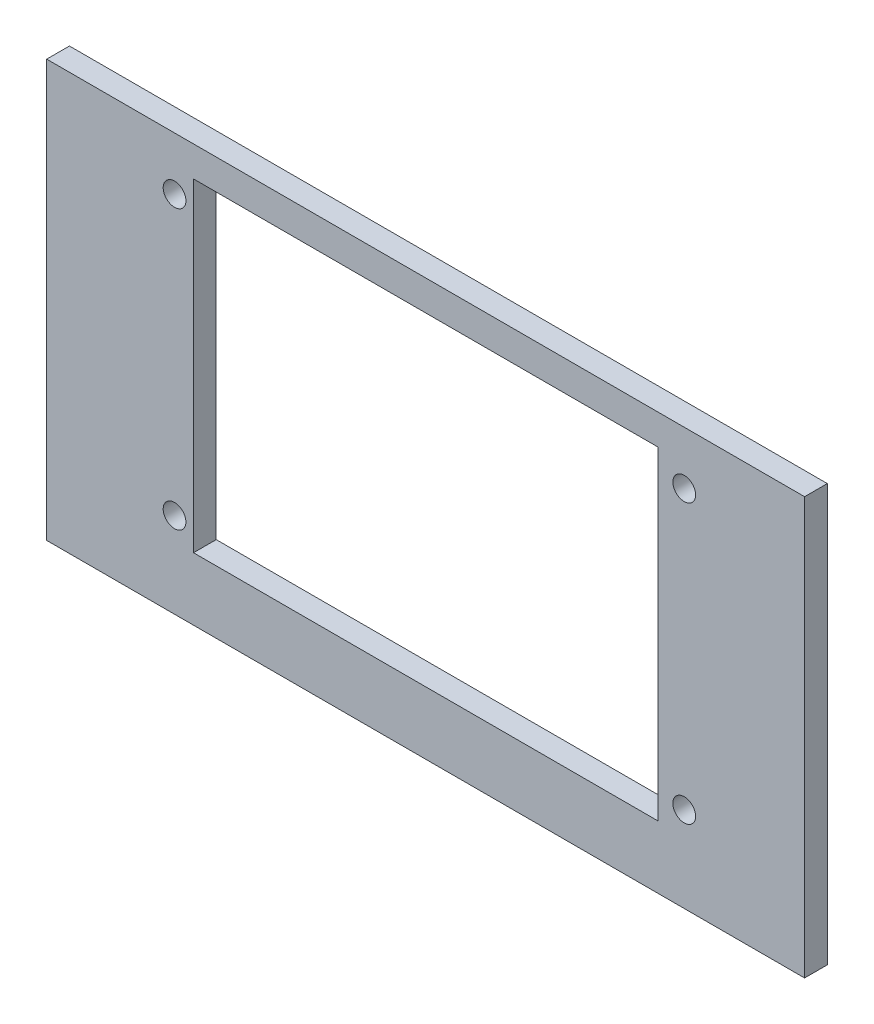
SolidWorks part; units mm, degrees
ref_plane "Front Plane" through (0, 0, 0) normal (0, 0, 1) x (1, 0, 0)
ref_plane "Top Plane" through (0, 0, 0) normal (0, 1, 0) x (1, 0, 0)
ref_plane "Right Plane" through (0, 0, 0) normal (1, 0, 0) x (0, 0, -1)
sketch "Sketch1" plane through (0, 0, 0) normal (0, 0, 1) x (1, 0, 0)
  line L1 (0, 0) -> (100, 0)
  line L2 (0, 0) -> (0, 55)
  line L3 (0, 55) -> (100, 55)
  line L4 (100, 0) -> (100, 55)
  line L5 (0, 0) -> (100, 55) construction
  line L6 (0, 55) -> (100, 0) construction
  line L7 (19.37, 8.28) -> (80.63, 8.28)
  line L8 (19.37, 8.28) -> (19.37, 51)
  line L9 (19.37, 51) -> (80.63, 51)
  line L10 (80.63, 8.28) -> (80.63, 51)
  line L11 (19.37, 8.28) -> (80.63, 51) construction
  line L12 (19.37, 51) -> (80.63, 8.28) construction
  circle A0 centre (84.12, 48) radius 1.5
  circle A1 centre (16.87, 48) radius 1.5
  circle A2 centre (16.87, 11.28) radius 1.5
  circle A3 centre (84.12, 11.28) radius 1.5
  point P4 (50, 27.5)
  point P10 (50, 29.64)
  point P19 (9.865, 46.8448)
  point P20 (0, 0)
  point P21 (0, 0)
  point P22 (0, 0)
  dimension "D5" = 3
  dimension "D6" = 3
  dimension "D8" = 3
  dimension "D12" = 3
  dimension "D1" = 100
  dimension "D2" = 55
  dimension "D3" = 61.26
  dimension "D4" = 42.72
  dimension "D7" = 3
  dimension "D9" = 3
  dimension "D10" = 2.5
  dimension "D11" = 2.5
  dimension "D13" = 4
  dimension "D14" = 19.37
  dimension "D15" = 3.49
extrude "Boss-Extrude1" add sketch "Sketch1" along normal blind 3
equation "\"x\"=18.3922"
